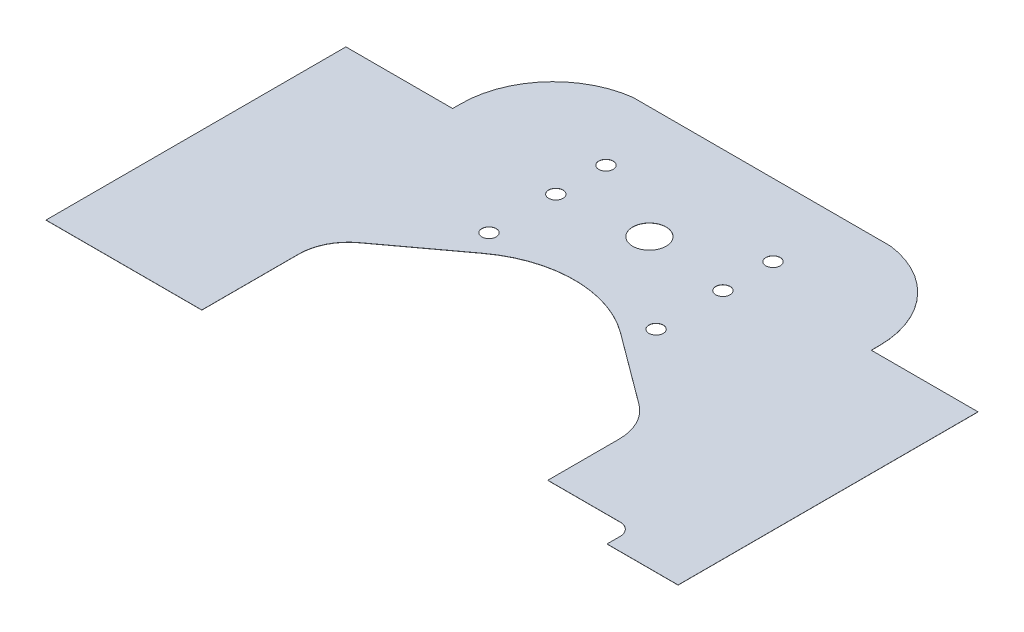
SolidWorks part; units mm, degrees
ref_plane "Front Plane" through (0, 0, 0) normal (0, 0, 1) x (1, 0, 0)
ref_plane "Top Plane" through (0, 0, 0) normal (0, 1, 0) x (1, 0, 0)
ref_plane "Right Plane" through (0, 0, 0) normal (1, 0, 0) x (0, 0, -1)
sketch "Sketch1" plane through (0, 0, 0) normal (0, 1, 0) x (1, 0, 0)
  line B0 (46.0556, -52.1025) -> (46.0556, -55.1058)
  line B1 (46.0556, -55.1058) -> (60.06, -55.1058)
  line B2 (60.06, -55.1058) -> (60.06, 2.3825)
  line B3 (60.06, 2.3825) -> (39.775, 2.3825)
  line B4 (39.775, 2.3825) -> (39.775, 3.9425)
  line B5 (-39.775, 3.9425) -> (-39.775, 2.3825)
  line B6 (-39.775, 2.3825) -> (-60.06, 2.3825)
  line B7 (-60.06, 2.3825) -> (-60.06, -55.1058)
  line B8 (-60.06, -55.1058) -> (-29.949, -55.1058)
  line B9 (-29.949, -55.1058) -> (-29.949, -36.195)
  line B10 (-26.3268, -29.0041) -> (-12.7672, -18.9597)
  line B11 (12.7672, -18.9597) -> (26.3268, -29.0041)
  line B12 (29.949, -36.195) -> (29.949, -50.2526)
  line B13 (29.949, -50.2526) -> (44.2056, -50.2526)
  circle B14 centre (-15.875, -1.905) radius 1.37
  circle B15 centre (-15.875, 7.62) radius 1.37
  circle B16 centre (-15.875, -14.605) radius 1.37
  circle B17 centre (0, 0) radius 3.175
  circle B18 centre (15.875, -1.905) radius 1.37
  circle B19 centre (15.875, 7.62) radius 1.37
  circle B20 centre (15.875, -14.605) radius 1.37
  arc B21 (46.0556, -52.1025) -> (44.2056, -50.2526) centre (44.2056, -52.1025) ccw
  arc B22 (39.775, 3.9425) -> (24.4755, 21.3476) centre (22.225, 3.9425) ccw
  arc B23 (-24.4755, 21.3476) -> (-39.775, 3.9425) centre (-22.225, 3.9425) ccw
  arc B24 (-26.3268, -29.0041) -> (-29.949, -36.195) centre (-21, -36.195) ccw
  arc B25 (12.7672, -18.9597) -> (-12.7672, -18.9597) centre (0, -36.195) ccw
  arc B26 (29.949, -36.195) -> (26.3268, -29.0041) centre (21, -36.195) ccw
  line B27 (-24.4755, 21.3476) -> (24.4755, 21.3476)
sketch_block_instance "BLOCK, Rear Diamond Plate-1"
sketch_block "BLOCK, Rear Diamond Plate"
extrude "Boss-Extrude1" add sketch "Sketch1" along normal blind 0.0254
sketch "Sketch2" plane through (0, 0.0254, 0) normal (0, 1, 0) x (1, 0, 0)
  line L0 (-60.06, -55.1058) -> (-29.949, -55.1058) construction
  line L1 (-29.949, -55.1058) -> (-29.949, -36.195) construction
  line L2 (-26.3268, -29.0041) -> (-12.7672, -18.9597) construction
  line L3 (12.7672, -18.9597) -> (26.3268, -29.0041) construction
  line L4 (29.949, -36.195) -> (29.949, -50.2526) construction
  line L5 (29.949, -50.2526) -> (44.2056, -50.2526) construction
  line L6 (46.0556, -52.1025) -> (46.0556, -55.1058) construction
  line L7 (46.0556, -55.1058) -> (60.06, -55.1058) construction
  line L8 (-60.06, -55.1058) -> (-29.949, -55.1058)
  line L9 (-29.949, -55.1058) -> (-29.949, -36.195)
  line L10 (-26.3268, -29.0041) -> (-12.7672, -18.9597)
  line L11 (12.7672, -18.9597) -> (26.3268, -29.0041)
  line L12 (29.949, -36.195) -> (29.949, -50.2526)
  line L13 (29.949, -50.2526) -> (44.2056, -50.2526)
  line L14 (46.0556, -52.1025) -> (46.0556, -55.1058)
  line L15 (46.0556, -55.1058) -> (60.06, -55.1058)
  line L16 (-60.06, -54.6058) -> (-30.449, -54.6058)
  line L17 (-30.449, -54.6058) -> (-30.449, -36.195)
  line L18 (-26.6244, -28.6023) -> (-13.0649, -18.5579)
  line L19 (13.0649, -18.5579) -> (26.6244, -28.6023)
  line L20 (30.449, -36.195) -> (30.449, -49.7526)
  line L21 (30.449, -49.7526) -> (44.2056, -49.7526)
  line L22 (46.5556, -52.1025) -> (46.5556, -54.6058)
  line L23 (46.5556, -54.6058) -> (60.06, -54.6058)
  line L24 (60.06, -54.6058) -> (60.06, -55.1058)
  line L25 (-60.06, -54.6058) -> (-60.06, -55.1058)
  arc A0 (-26.3268, -29.0041) -> (-29.949, -36.195) centre (-21, -36.195) ccw construction
  arc A1 (12.7672, -18.9597) -> (-12.7672, -18.9597) centre (0, -36.195) ccw construction
  arc A2 (29.949, -36.195) -> (26.3268, -29.0041) centre (21, -36.195) ccw construction
  arc A3 (46.0556, -52.1025) -> (44.2056, -50.2526) centre (44.2056, -52.1025) ccw construction
  arc A4 (-26.3268, -29.0041) -> (-29.949, -36.195) centre (-21, -36.195) ccw
  arc A5 (12.7672, -18.9597) -> (-12.7672, -18.9597) centre (0, -36.195) ccw
  arc A6 (29.949, -36.195) -> (26.3268, -29.0041) centre (21, -36.195) ccw
  arc A7 (46.0556, -52.1025) -> (44.2056, -50.2526) centre (44.2056, -52.1025) ccw
  arc A8 (-26.6244, -28.6023) -> (-30.449, -36.195) centre (-21, -36.195) ccw
  arc A9 (13.0649, -18.5579) -> (-13.0649, -18.5579) centre (0, -36.195) ccw
  arc A10 (30.449, -36.195) -> (26.6244, -28.6023) centre (21, -36.195) ccw
  arc A11 (46.5556, -52.1025) -> (44.2056, -49.7526) centre (44.2056, -52.1025) ccw
  dimension "D1" = 0.5
extrude "Cut-Extrude1" cut sketch "Sketch2" against normal through all
